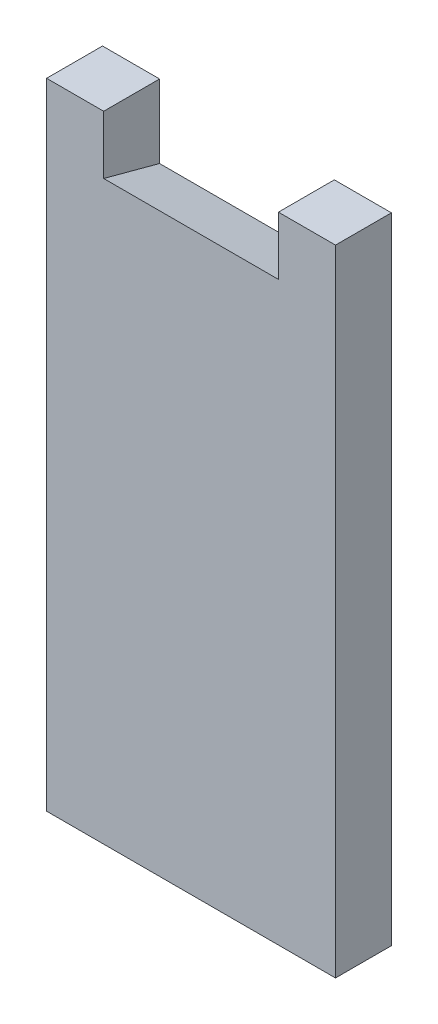
SolidWorks part; units mm, degrees
ref_plane "前视基准面" through (0, 0, 0) normal (0, 0, 1) x (1, 0, 0)
ref_plane "上视基准面" through (0, 0, 0) normal (0, 1, 0) x (1, 0, 0)
ref_plane "右视基准面" through (0, 0, 0) normal (1, 0, 0) x (0, 0, -1)
sketch "草图1" plane through (0, 0, 0) normal (0, 0, 1) x (1, 0, 0)
  line L1 (0, 0) -> (49.6, 0)
  line L2 (0, 0) -> (0, -108.97)
  line L3 (0, -108.97) -> (49.6, -108.97)
  line L4 (49.6, 0) -> (49.6, -108.97)
  line L5 (9.8, 0) -> (39.8, 0)
  line L6 (9.8, 0) -> (9.8, -10)
  line L7 (9.8, -10) -> (39.8, -10)
  line L8 (39.8, 0) -> (39.8, -10)
  point P9 (24.8, 0)
  dimension "D1" = 10
  dimension "D2" = 49.6
  dimension "D3" = 30
  dimension "D4" = 98.97
extrude "凸台-拉伸1" add sketch "草图1" along normal blind 9.6 contours L1 L8 L7 L6 L2 L3 L4
draft "拔模5" type of draft neutral plane draft angle 15 faces to draft 1 face at (24.8, -10, 4.8) neutral plane through (0, 0, 9.6) neutral plane normal (0, 0, 1) reverse direction yes parameters "D1"=15
